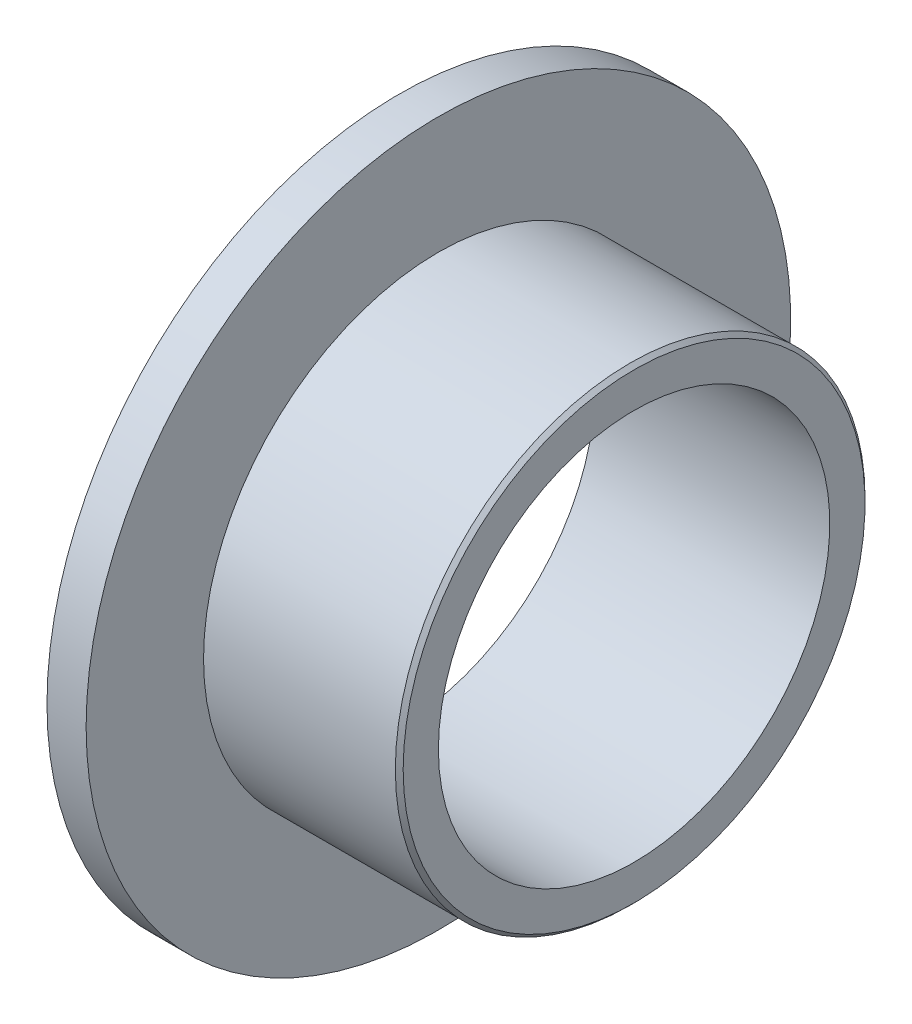
SolidWorks part; units mm, degrees
ref_plane "前视基准面" through (0, 0, 0) normal (0, 0, 1) x (1, 0, 0)
ref_plane "上视基准面" through (0, 0, 0) normal (0, 1, 0) x (1, 0, 0)
ref_plane "右视基准面" through (0, 0, 0) normal (1, 0, 0) x (0, 0, -1)
ref_plane "基准面1" through (0, 0, 0) normal (0, 0, -1) x (-1, 0, 0)
sketch "草图1" plane through (0, 0, 0) normal (0, 0, -1) x (-1, 0, 0)
  line L0 (0, 9) -> (-1, 9)
  line L1 (-1, 9) -> (-1, 6)
  line L2 (-1, 6) -> (-5.9, 6)
  line L3 (-5.9, 6) -> (-6, 5.9)
  line L4 (-6, 5.9) -> (-6, 5)
  line L5 (-6, 5) -> (0, 5)
  line L6 (0, 5) -> (0, 9)
  line L7 (-4, 0) -> (0, 0) construction
  dimension "D1" = 12
  dimension "D2" = 10
  dimension "D3" = 1
  dimension "D4" = 4
  dimension "D5" = 0.1414
  dimension "D6" = 45
  dimension "D7" = 6
  dimension "D8" = 18
revolve "旋转1" add sketch "草图1" angle 360 about L7
sketch "草图2" plane through (0, 0, 0) normal (-1, 0, 0) x (0, 0, 1)
  circle A0 centre (0, 0) radius 1.4
  dimension "D1" = 2.8
